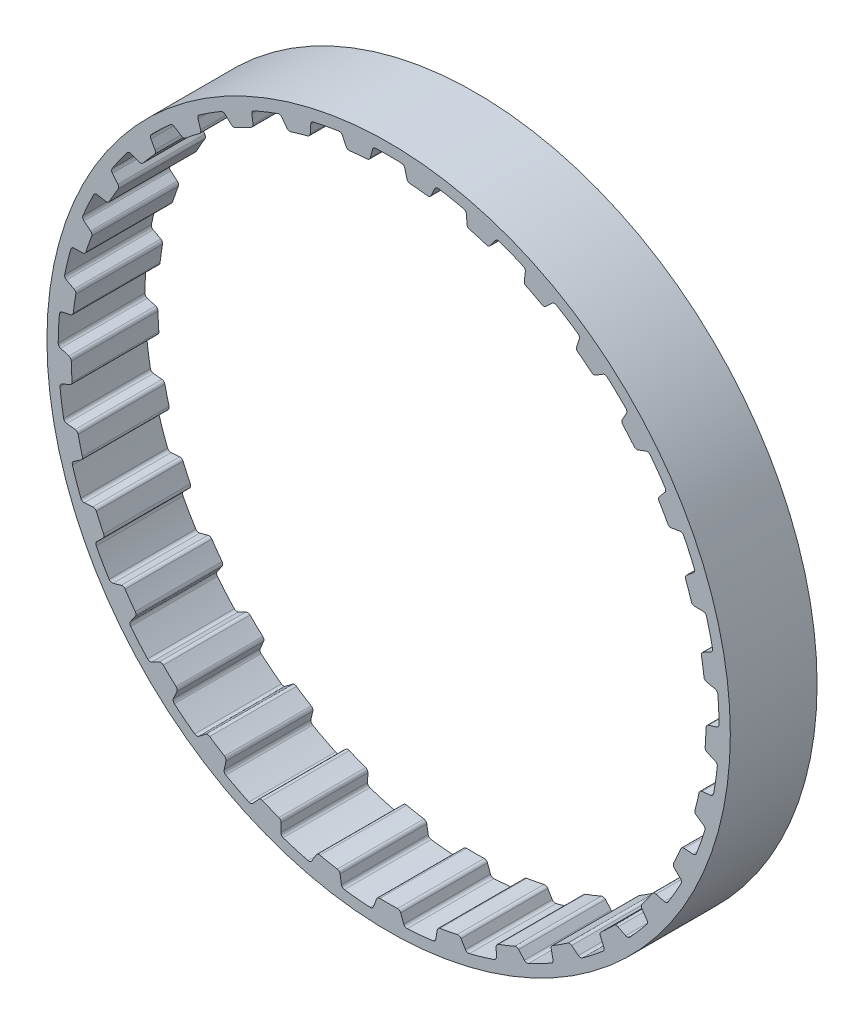
SolidWorks part; units mm, degrees
ref_plane "Front Plane" through (0, 0, 0) normal (0, 0, 1) x (1, 0, 0)
ref_plane "Top Plane" through (0, 0, 0) normal (0, 1, 0) x (1, 0, 0)
ref_plane "Right Plane" through (0, 0, 0) normal (1, 0, 0) x (0, 0, -1)
sketch "Sketch1" plane through (0, 0, 0) normal (0, 0, 1) x (1, 0, 0)
  line L0 (0, 0) -> (-4.4173, 46.26) construction
  line L1 (0, 0) -> (4.4173, 46.26) construction
  line L2 (4.4173, 46.26) -> (-4.4173, 46.26) construction
  line L3 (4.4173, 46.26) -> (-4.4173, 46.26) construction
  circle A0 centre (0, 0) radius 50.0264
  circle A1 centre (0, 0) radius 46.4704
  circle A2 centre (0, 0) radius 48.3754 construction
  dimension "OD" = 100.0528
  dimension "Angle Distance" = 10.909
  dimension "hs" = 3.556
  dimension "ht" = 1.905
extrude "Boss-Extrude1" add sketch "Sketch1" along normal mid plane 12.7
sketch "Sketch2" plane through (0, 0, 0) normal (0, 0, 1) x (1, 0, 0)
  line L1 (0, 50.0264) -> (0, 0) construction
  line L2 (-4.7625, 47.3701) -> (4.7625, 47.3701) construction
  line L4 (-2.763, 46.418) -> (-6.0716, 46.102)
  line L5 (-2.763, 46.418) -> (-2.2689, 48.3222)
  line L6 (-6.0716, 46.102) -> (-6.9171, 47.8783)
  line L7 (0, 0) -> (-4.4173, 46.26) construction
  line L8 (-2.2689, 48.3222) -> (-6.9171, 47.8783) construction
  line L9 (2.2689, 48.3222) -> (6.9171, 47.8783) construction
  line L10 (6.0716, 46.102) -> (6.9171, 47.8783)
  line L11 (2.763, 46.418) -> (2.2689, 48.3222)
  line L12 (2.763, 46.418) -> (6.0716, 46.102)
  line L13 (0, 0) -> (19.1443, 46.2184) construction
  line L14 (-4.7625, 47.3701) -> (-14.0969, 45.474) construction
  line L15 (-9.4297, 46.422) -> (0, 0) construction
  line L16 (-14.0969, 45.474) -> (-13.7598, 44.3866) construction
  circle A0 centre (0, 0) radius 48.3754 construction
  circle A1 centre (0, 0) radius 48.3754
  circle A2 centre (0, 0) radius 47.3701 construction
  circle A4 centre (0, 0) radius 50.0264 construction
  circle A5 centre (0, 0) radius 46.4704 construction
  point P16 (-2.516, 47.3701)
  point P20 (0, 47.3701)
  dimension "D1" = 22.5
  dimension "bt" = 4.6482
  dimension "b" = 40
  dimension "Pitch" = 9.525
sketch "Sketch3" plane through (0, 0, 0) normal (0, 0, 1) x (1, 0, 0)
  line L0 (-3.1359, 46.3645) -> (3.1359, 46.3645)
  line L2 (-2.763, 46.418) -> (-2.2689, 48.3222) construction
  line L3 (2.763, 46.418) -> (2.2689, 48.3222) construction
  line L5 (-2.6785, 46.7437) -> (-2.3633, 47.9584)
  line L7 (2.6785, 46.7437) -> (2.3633, 47.9584)
  arc A0 (2.6785, 46.7437) -> (3.1359, 46.3645) centre (3.1702, 46.8713) ccw
  circle A1 centre (0, 0) radius 48.3754 construction
  arc A2 (1.8915, 48.3384) -> (-1.8915, 48.3384) centre (0, 0) ccw
  arc A3 (-2.6785, 46.7437) -> (-3.1359, 46.3645) centre (-3.1702, 46.8713) cw
  arc A4 (2.3633, 47.9584) -> (1.8915, 48.3384) centre (1.8716, 47.8308) ccw
  arc A5 (-2.3633, 47.9584) -> (-1.8915, 48.3384) centre (-1.8716, 47.8308) cw
  circle A6 centre (0, 0) radius 46.4704 construction
  arc A7 (-3.1359, 46.3645) -> (3.1359, 46.3645) centre (0, 0) ccw construction
  dimension "ra" = 0.508
  dimension "rr" = 0.508
extrude "Cut-Extrude1" cut sketch "Sketch3" against normal mid plane 12.7
pattern_circular "CirPattern1" count 33 over 360 about axis through (0, 0, 0) along (0, 0, 1) of "Cut-Extrude1"
equation "\"D1@Cut-Extrude1\" = \"Width@Boss-Extrude1\""
